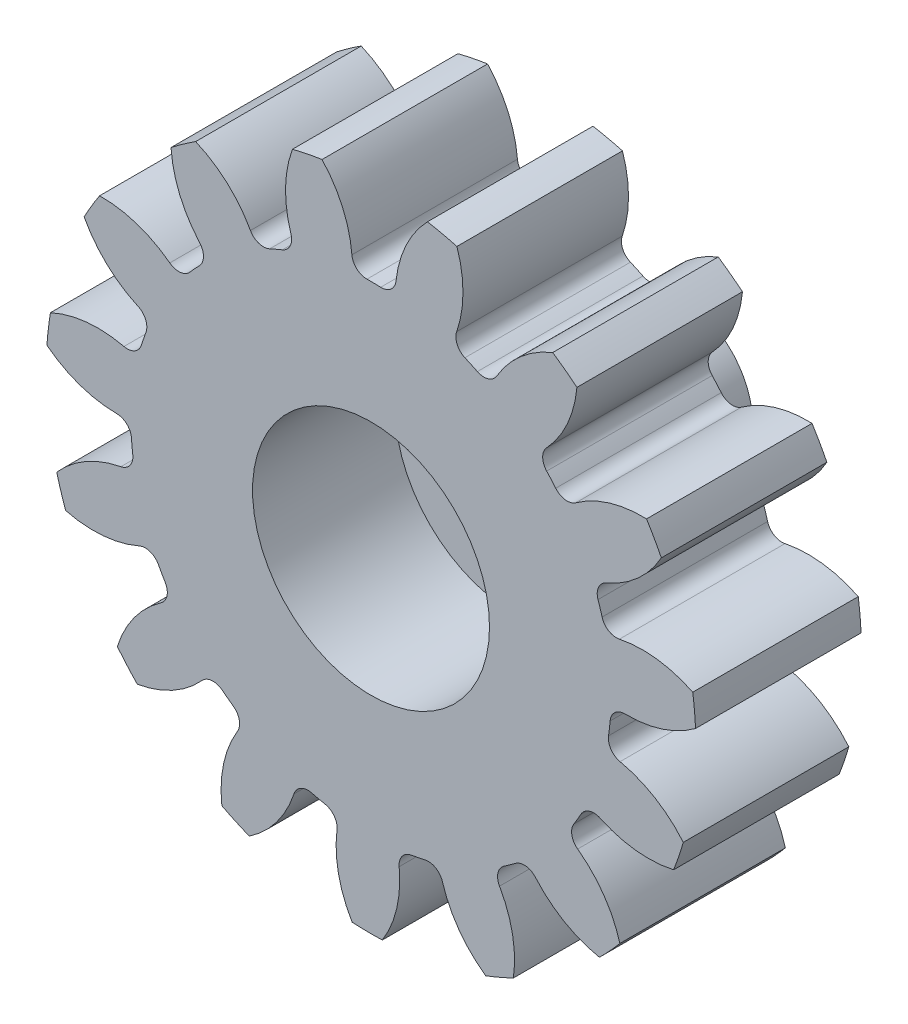
SolidWorks part; units mm, degrees
material "ABS"
ref_plane "Front" through (0, 0, 0) normal (0, 0, 1) x (1, 0, 0)
ref_plane "Top" through (0, 0, 0) normal (0, 1, 0) x (1, 0, 0)
ref_plane "Right" through (0, 0, 0) normal (1, 0, 0) x (0, 0, -1)
sketch "Sketch3" plane through (0, 0, 0) normal (0, 0, 1) x (1, 0, 0)
  circle A0 centre (0, 0) radius 21.59
  dimension "od" = 43.18
extrude "gearBody" add sketch "Sketch3" along normal blind 11
sketch "Sketch2" plane through (0, 0, 0) normal (0, 0, 1) x (1, 0, 0)
  line L0 (0, 0) -> (17.0393, 7.0579) construction
  line L1 (22.0105, -8.0941) -> (0, 0) construction
  line L2 (0, 0) -> (36.3143, 0) construction
  line L3 (19.0486, -0.229) -> (18.5878, -4.1711) construction
  line L5 (18.8182, -2.2) -> (0, 0) construction
  line L7 (0, 0) -> (18.4432, 0) construction
  arc A0 (18.4395, -0.3701) -> (18.0276, -3.8932) centre (0, 0) ccw construction
  arc A1 (21.5666, 1.0048) -> (20.7532, -5.9524) centre (0, 0) ccw construction
  arc A2 (19.0486, -0.229) -> (18.5878, -4.1711) centre (0, 0) ccw construction
  arc A3 (15.7838, -2.3046) -> (15.8898, -1.3984) centre (0, 0) ccw
  arc A4 (22.0105, -8.0941) -> (16.5506, -3.4102) centre (14.9518, -10.798) ccw
  arc A5 (22.0105, -8.0941) -> (23.2839, 2.7987) centre (0, 0) ccw
  arc A6 (23.2839, 2.7987) -> (16.8909, -0.4995) centre (17.0393, 7.0579) cw
  arc A7 (15.8898, -1.3984) -> (16.8909, -0.4995) centre (16.8715, -1.4848) cw
  arc A8 (16.5506, -3.4102) -> (15.7838, -2.3046) centre (16.759, -2.4469) cw
  point P6 (23.2839, 2.7987)
  point P22 (22.0105, -8.0941)
  dimension "baseDia" = 36.8864
  dimension "od" = 43.18
  dimension "pd" = 38.1
  dimension "rd" = 31.9024
  dimension "rFillet" = 0.9855
  dimension "pointX" = 23.2839
  dimension "pointY" = 2.7987
  dimension "CTT" = 3.9421
  dimension "flankCenterAngle" = 22.5
extrude "toothCut" cut sketch "Sketch2" along normal through all
pattern_circular "CirPattern1" count 15 over 360 about axis through (0, 0, 0) along (0, 0, 1) of "toothCut"
sketch "hub1Dia" plane through (0, 0, 0) normal (0, 0, -1) x (-1, 0, 0)
  circle A0 centre (0, 0) radius 12.7
  dimension "hub1Dia" = 25.4
sketch "hub2Dia" plane through (0, 0, 11) normal (0, 0, 1) x (1, 0, 0)
  circle A0 centre (0, 0) radius 12.7
  dimension "hub2dia" = 25.4
sketch "boreDia" plane through (0, 0, 0) normal (0, 0, 1) x (1, 0, 0)
  circle A0 centre (0, 0) radius 7.874
  dimension "boreDia" = 15.748
extrude "bore" cut sketch "boreDia" against normal mid plane 25400
sketch "Sketch4" plane through (0, 0, 0) normal (1, 0, 0) x (0, 0, -1)
  line L0 (0, 0) -> (29.4347, 0) construction
  line L1 (0, 0) -> (9.525, 0)
  line L2 (9.525, 0) -> (9.525, 4.826)
  line L3 (9.525, 4.826) -> (5.588, 4.826)
  line L4 (0, 0) -> (-1.524, 0)
  line L5 (-1.524, 0) -> (-1.524, 7.874)
  line L6 (-1.524, 7.874) -> (0, 7.874)
  line L7 (0, 12.2181) -> (0, 16.6995) construction
  line L8 (0, 7.874) -> (0, 10.414)
  arc A0 (0, 10.414) -> (5.588, 4.826) centre (5.588, 10.414) ccw
  dimension "D3" = 5.588
  dimension "D1" = 15.748
  dimension "D2" = 9.652
  dimension "D4" = 1.524
  dimension "D5" = 9.525
revolve "Revolve1" add sketch "Sketch4" angle 360 about L0
sketch "Sketch6" plane through (0, 0, -9.525) normal (0, 0, -1) x (-1, 0, 0)
  circle A0 centre (0, 0) radius 4.1
  dimension "D1" = 8.2
extrude "Cut-Extrude1" cut sketch "Sketch6" against normal blind 5.3
equation "\"Mid_Tube_Length\"= 1in"
equation "\"Bodytube_OD\"= 6.17in"
equation "\"Bodytube_ID\"= 5.998in"
equation "\"Camera_Cutout_Width\"=10mm"
equation "\"Camera_Cutout_Height\"=7mm"
equation "\"Fwd_Tube_Length\"= 40in"
equation "\"BKHD_Screw_Diam\"= 3.5mm"
equation "\"Fwd_BKHD_From_Top\"= 18in"
equation "\"Shear_Screw_Diameter\"= 0.086in"
equation "\"Shear_Screw_Coupler_Location\"= 4.5in"
equation "\"Motor_OD\"= 4in"
equation "\"Mid_Coupler_Length\"= 13in"
equation "\"Aft_Section_Length\"= 39in"
equation "\"AB_Coupler_OD_Length\"= 1in"
equation "\"AB_Coupling_Section_Length\"= 0.375in"
equation "\"AB_Coupler_Length\"= \"AB_Coupler_OD_Length\" + \"AB_Coupling_Section_Length\" * 2"
equation "\"Cutout_Angle\"= 80"
equation "\"AB_Paddle_Height\"= 0.375in"
equation "\"AB_Coupler_Num_Screws\"= 4"
equation "\"AB_BKHD_Thickness\"= 0.375in"
equation "\"AB_Mount_From_Bottom\"= 23.175in"
equation "\"Num_Cutouts\"= 3"
equation "\"AB_Coupler_OD\"= 6.17in"
equation "\"AB_Coupler_ID\"= 5.75in"
equation "\"AB_Coupler_Surface_Diameter\"= 5.998in"
equation "\"AB_Coupling_Screw_Diameter\"= 0.15748in"
equation "\"AB_Central_Bushing_Length\"= .4724in"
equation "\"Lead_Screw_Dist\"= 3.4in"
equation "\"Lead_Screw_Diam\"= 0.386in"
equation "\"Lead_Screw_Length\"= (\"Mid_Coupler_Length\" + 2*0.375in + 2*0.5in)"
equation "\"Paddle_Pin_Offset\"= .25in"
equation "\"Paddle_Pin_Radius\"= 2.25in"
equation "\"SS_Paddle_Pin_Radius\"= 2.25*0.66in"
equation "\"Paddle_Gear_OD\"= 3.2in"
equation "\"Drive_Gear_OD\"= 1.7in"
equation "\"Fin_Thickness\"= .118in"
equation "\"Guiderail_Cutout_Diameter\"= 1.5in"
equation "\"DB9_Hole_Dist\"= 25mm"
equation "\"DB9_Relief_Width\"= 0.47in"
equation "\"DB9_Relief_Hole_Offset\"= 0.09in"
equation "\"Airbrakes_Wire_Hole_Dia\"= .25in"
equation "\"Airbrakes_Wire_Hole_Dist\"= 1.1in"
equation "\"Servo_Gear_Offset\"= 0.5in"
equation "\"FWD_Shear_Screw_Dist\"= 1.5in"
equation "\"Camera_Screw_Dia\"= 0.216535"
equation "\"Camera_Hole_Angle\"= atn ( 2 / 3 * tan ( 12.5deg ) )"
equation "\"Coupler_OD\"= 5.998"
equation "\"Coupler_ID\"= 5.8"
equation "\"Mounting_Bracket_Centerhole_DIA\"= 0.4in"
equation "\"Drive_Gear_Shaft_DIA\"= \"Mounting_Bracket_Centerhole_DIA\" - 0.02in"
equation "\"Drive_Gear_Fillet\"= 0.22in"
equation "\"Drive_Gear_ID\"= 0.62in"
equation "\"Drive_Gear_Offset\"= 0.01in"
equation "\"D2@Sketch4\"=\"Drive_Gear_Shaft_DIA\""
equation "\"D1@Sketch4\"=\"Drive_Gear_ID\""
equation "\"D3@Sketch4\"=\"Drive_Gear_Fillet\""
